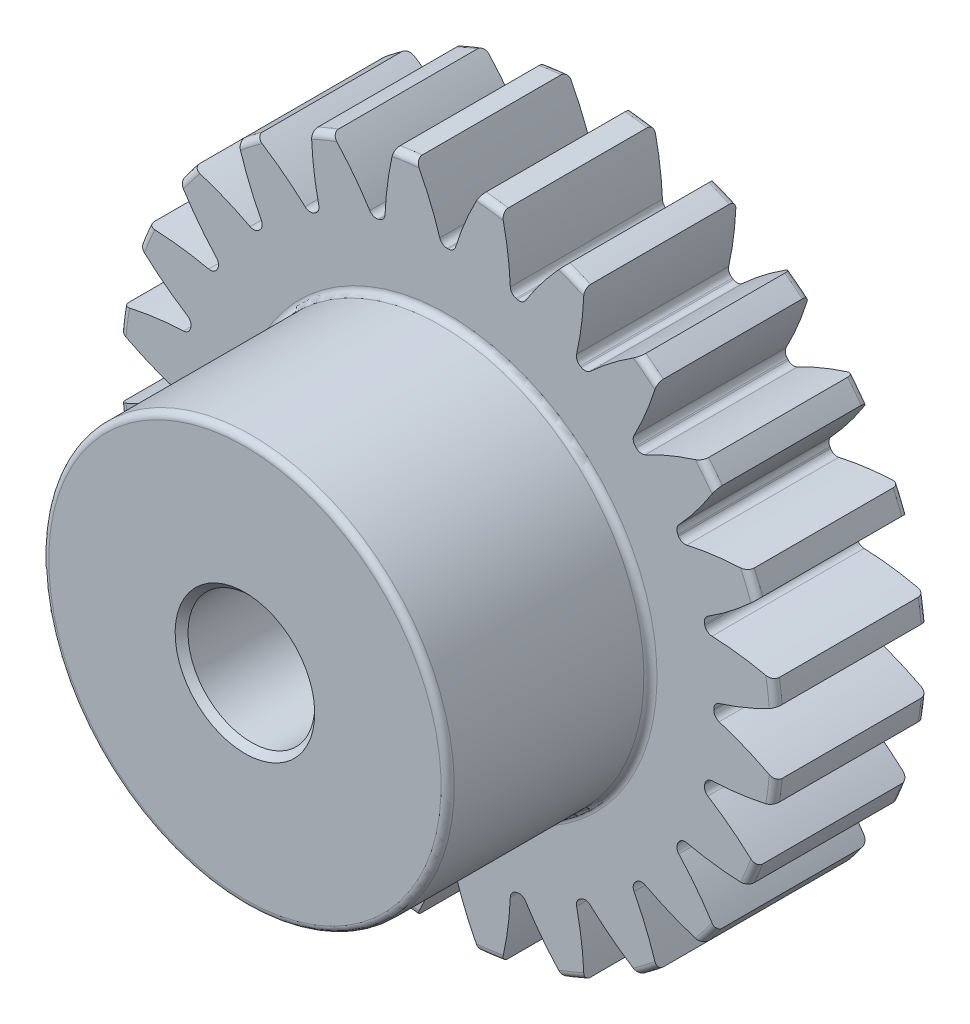
SolidWorks part; units mm, degrees
material "ABS"
ref_plane "Front Plane" through (0, 0, 0) normal (0, 0, 1) x (1, 0, 0)
ref_plane "Top Plane" through (0, 0, 0) normal (0, 1, 0) x (1, 0, 0)
ref_plane "Right Plane" through (0, 0, 0) normal (1, 0, 0) x (0, 0, -1)
sketch "Sketch1" plane through (0, 0, 0) normal (0, 0, 1) x (1, 0, 0)
  line L0 (-304.8, 0) -> (304.8, 0) construction
  circle A0 centre (0, 0) radius 6.5 construction
  circle A1 centre (0, 0) radius 6 construction
  circle A2 centre (0, 0) radius 5.25 construction
  circle A3 centre (0, 0) radius 4 construction
  circle A4 centre (0, 0) radius 2 construction
  dimension "D2" = 0.5
  dimension "D3" = 1.25
  dimension "D1" = 1.25
sketch "Sketch2" plane through (0, 0, 0) normal (1, 0, 0) x (0, 0, -1)
  line L0 (0, 0) -> (-3, 0) construction
  line L1 (-3, 0) -> (-7, 0) construction
  dimension "Overall Width" = 7
  dimension "Face Width" = 3
sketch "Sketch4" plane through (0, 0, 0) normal (1, 0, 0) x (0, 0, -1)
  line L0 (-7, 2) -> (-7, 4)
  line L1 (-7, 4) -> (-3, 4)
  line L2 (-3, 4) -> (-3, 6.5)
  line L3 (-3, 6.5) -> (0, 6.5)
  line L4 (0, 6.5) -> (0, 2)
  line L5 (-3, 4) -> (-3, 0) construction
  line L6 (0, 6.5) -> (0, -6.5) construction
  line L7 (-3, 4) -> (0, 4) construction
  line L12 (-7, 2) -> (0, 2)
revolve "Revolve1" add sketch "Sketch4" angle 360 about L1
fillet "Fillet2" radius 0.13 4 edges at (0, 4, 7) (0, 4, 3) (0, 6.5, 3) (0, 6.5, 0)
sketch "Sketch7" plane through (0, 0, 3) normal (0, 0, 1) x (1, 0, 0)
  line L0 (0, 0) -> (0, 6.5) construction
  line L1 (0.3924, 5.9872) -> (0.6056, 6.4717) construction
  line L3 (0.8484, 6.4444) -> (0.7832, 5.9487) construction
  line L4 (0.7832, 5.9487) -> (0.6853, 5.2051) construction
  line L5 (0, 0) -> (0.6853, 5.2051) construction
  line L6 (0.3924, 5.9872) -> (0, 0) construction
  line L7 (0.3924, 5.9872) -> (0.4251, 6.4861) construction
  line L8 (0.3924, 5.9872) -> (0, 0) construction
  circle A0 centre (0, 0) radius 6.5 construction
  arc A1 (-0.0123, 5.25) -> (0.0123, 5.25) centre (0, 0) cw
  circle A2 centre (0, 0) radius 5.25 construction
  arc A3 (-0.3924, 5.9872) -> (0.3924, 5.9872) centre (0, 0) cw construction
  circle A4 centre (0, 0) radius 6 construction
  arc A5 (1.065, 6.4122) -> (0.6309, 6.4693) centre (0, 0) ccw construction
  arc A6 (0.3924, 5.9872) -> (1.1705, 5.8847) centre (0, 0) cw construction
  arc A7 (-0.6309, 6.4693) -> (0.6309, 6.4693) centre (0, 0) cw
  arc A8 (0.1559, 5.3554) -> (0.6309, 6.4693) centre (5.8843, 3.5707) cw
  arc A9 (-0.1559, 5.3554) -> (-0.6309, 6.4693) centre (-5.8843, 3.5707) ccw
  arc A10 (-0.0123, 5.25) -> (-0.1559, 5.3554) centre (-0.0126, 5.4) cw
  arc A11 (0.0123, 5.25) -> (0.1559, 5.3554) centre (0.0126, 5.4) ccw
  point P26 (-0.1237, 5.2485)
  point P29 (0.1237, 5.2485)
  dimension "D4" = 0.15
  dimension "D5" = 6
  dimension "D3" = 20
  dimension "D1" = 1.5708
  dimension "D2" = 0.7854
extrude "Cut-Extrude2" cut sketch "Sketch7" against normal through all
pattern_circular "CirPattern1" count 24 over 360 about axis through (0, 0, 0) along (0, 0, 1) of "Cut-Extrude2"
sketch "Sketch9" plane through (0, 0, 0) normal (0, 0, -1) x (-1, 0, 0)
  circle A0 centre (0, 0) radius 2
  circle A1 centre (0, 0) radius 2 construction
  circle A2 centre (0, 0) radius 1.25
  dimension "D1" = 2.5
extrude "Boss-Extrude1" add sketch "Sketch9" against normal up to surface (7 mm away) up to face at (0, -3.87, 7)
chamfer "Chamfer1" distance 0.127 angle 45 2 edges at (0, 1.25, 0) (0, -1.25, 7)
equation "\"D1@Sketch1\"=2.5*(\"Pitch Dia.@Sketch1\"/\"Number of Teeth@Sketch1\")"
equation "\"D1@CirPattern1\"=\"Number of Teeth@Sketch1\""
equation "\"D1@Fillet2\"=\"OD@Sketch1\"*.01"
equation "\"D1@Sketch7\"=3.14159*(\"Pitch Dia.@Sketch1\"/\"Number of Teeth@Sketch1\")"
equation "\"D2@Sketch7\"=\"D1@Sketch7\"/2"
equation "\"D4@Sketch7\"=\"D1@Sketch7\"*.0955"
equation "\"D5@Sketch7\"=\"Pitch Dia.@Sketch1\"/2"
